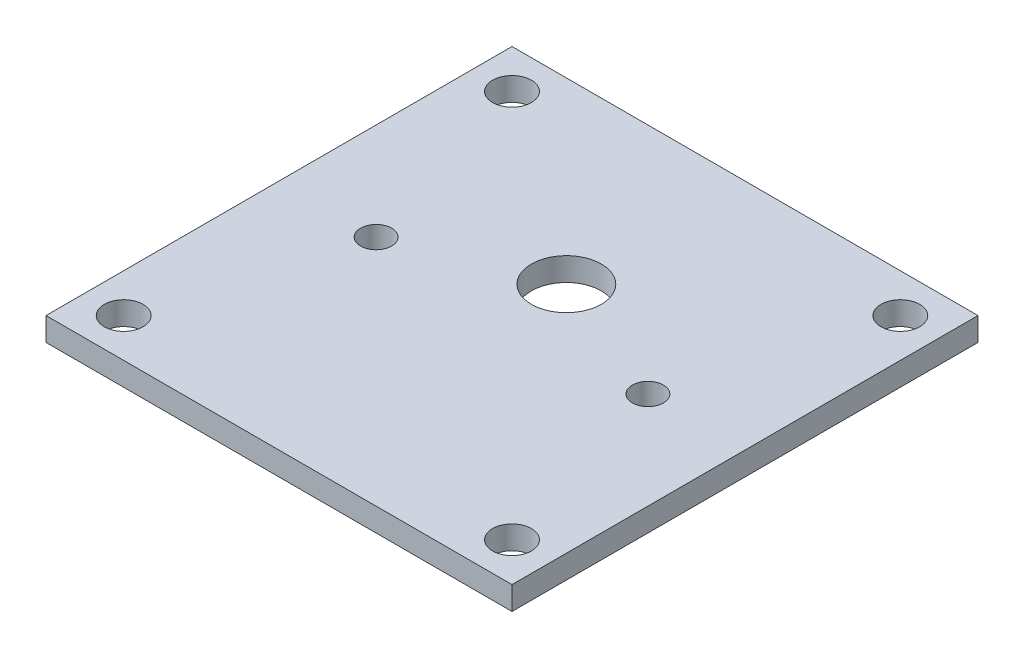
SolidWorks part; units mm, degrees
ref_plane "Front Plane" through (0, 0, 0) normal (0, 0, 1) x (1, 0, 0)
ref_plane "Top Plane" through (0, 0, 0) normal (0, 1, 0) x (1, 0, 0)
ref_plane "Right Plane" through (0, 0, 0) normal (1, 0, 0) x (0, 0, -1)
sketch "Sketch1" plane through (0, 0, 0) normal (0, 1, 0) x (1, 0, 0)
  line L0 (-30, 25) -> (30, 25) construction
  line L1 (-30, -30) -> (30, -30)
  line L2 (-30, -30) -> (-30, 30)
  line L3 (-30, 30) -> (30, 30)
  line L4 (30, -30) -> (30, 30)
  line L5 (-30, -30) -> (30, 30) construction
  line L6 (-30, 30) -> (30, -30) construction
  line L7 (-25, 30) -> (-25, -30) construction
  line L8 (-17.4954, -3.5) -> (-13.5554, -3.5)
  line L9 (-17.4954, 3.5) -> (-13.5554, 3.5)
  line L10 (0, 0) -> (0, -3.5) construction
  line L11 (17.4954, -3.5) -> (13.5554, -3.5)
  line L12 (17.4954, 3.5) -> (13.5554, 3.5)
  circle A0 centre (-25, 25) radius 2.5
  circle A1 centre (25, 25) radius 2.5
  circle A2 centre (25, -25) radius 2.5
  circle A3 centre (-25, -25) radius 2.5
  circle A8 centre (0, 0) radius 14
  circle A9 centre (0, 7) radius 4.5
  arc A10 (-17.4954, 3.5) -> (-17.4954, -3.5) centre (-17.4954, 0) ccw
  circle A11 centre (-17.4954, 0) radius 2
  circle A12 centre (17.4954, 0) radius 2
  arc A13 (17.4954, 3.5) -> (17.4954, -3.5) centre (17.4954, 0) cw
  arc A14 (-13.9991, -0.1597) -> (-13.9991, 0.1597) centre (-17.4954, 0) ccw
  arc A15 (13.9991, -0.1597) -> (13.9991, 0.1597) centre (17.4954, 0) cw
  point P0 (0, 0)
  dimension "D5" = 2
  dimension "D6" = 28
  dimension "D7" = 7
  dimension "D8" = 3.94
  dimension "D10" = 7
  dimension "D1" = 60
  dimension "D2" = 60
  dimension "D3" = 5
  dimension "D4" = 5
  dimension "D9" = 3.94
extrude "Boss-Extrude1" add sketch "Sketch1" along normal blind 3 contours L1 L4 L3 L2 A2 A1 A0 A3 L12 A13 L11 A8 L8 A10 L9 | A8 A15 A14 A9 | L9 A10 L8 A8 A11 | A13 L12 A8 L11 A12
